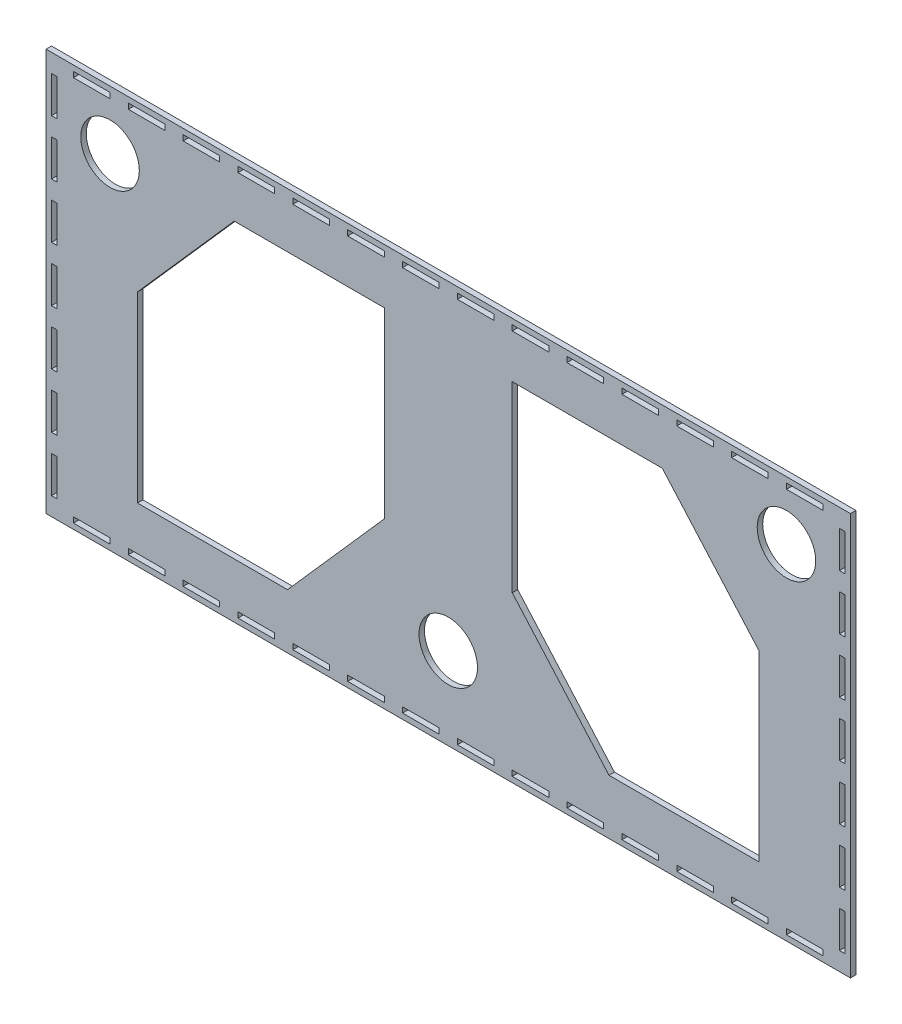
SolidWorks part; units mm, degrees
ref_plane "Plan de face" through (0, 0, 0) normal (0, 0, 1) x (1, 0, 0)
ref_plane "Plan de dessus" through (0, 0, 0) normal (0, 1, 0) x (1, 0, 0)
ref_plane "Plan de droite" through (0, 0, 0) normal (1, 0, 0) x (0, 0, -1)
sketch "Esquisse1" plane through (0, 0, 0) normal (0, 0, 1) x (1, 0, 0)
  line L1 (-220, 110) -> (220, 110)
  line L2 (-220, 110) -> (-220, -110)
  line L3 (-220, -110) -> (220, -110)
  line L4 (220, 110) -> (220, -110)
  line L5 (-220, 110) -> (220, -110) construction
  line L6 (-220, -110) -> (220, 110) construction
  point P0 (0, 0)
  dimension "D1" = 440
  dimension "D2" = 220
extrude "Boss.-Extru.1" add sketch "Esquisse1" along normal blind 3
sketch "Esquisse2" plane through (0, 0, 0) normal (0, 0, -1) x (-1, 0, 0)
  line L0 (0, 110) -> (0, -110) construction
  line L1 (-220, 110) -> (220, 110) construction
  line L2 (220, -110) -> (-220, -110) construction
  line L3 (-220, 0) -> (220, 0) construction
  line L4 (-220, -110) -> (-220, 110) construction
  line L5 (220, 110) -> (220, -110) construction
  circle A0 centre (-185, 78) radius 16
  circle A4 centre (185, 78) radius 16
  circle A7 centre (0, -65) radius 16
  point P18 (0, -66.7809)
  dimension "D1" = 32
  dimension "D2" = 32
  dimension "D3" = 35
  dimension "D5" = 32
  dimension "D4" = 45
extrude "Enlèv. mat._Tube" cut sketch "Esquisse2" against normal blind 3
sketch "Esquisse4" plane through (0, 0, 0) normal (0, 0, -1) x (-1, 0, 0)
  line L0 (-220, 110) -> (220, 110) construction
  line L1 (-205, 107) -> (-185, 107)
  line L2 (-205, 107) -> (-205, 104)
  line L3 (-205, 104) -> (-185, 104)
  line L4 (-185, 107) -> (-185, 104)
  line L5 (-220, -110) -> (-220, 110) construction
  line L6 (-175, 107) -> (-155, 107)
  line L7 (-175, 107) -> (-175, 104)
  line L8 (-175, 104) -> (-155, 104)
  line L9 (-155, 107) -> (-155, 104)
  line L10 (-145, 107) -> (-125, 107)
  line L11 (-145, 107) -> (-145, 104)
  line L12 (-145, 104) -> (-125, 104)
  line L13 (-125, 107) -> (-125, 104)
  line L14 (-115, 107) -> (-95, 107)
  line L15 (-115, 107) -> (-115, 104)
  line L16 (-115, 104) -> (-95, 104)
  line L17 (-95, 107) -> (-95, 104)
  line L18 (-85, 107) -> (-65, 107)
  line L19 (-85, 107) -> (-85, 104)
  line L20 (-85, 104) -> (-65, 104)
  line L21 (-65, 107) -> (-65, 104)
  line L22 (-55, 107) -> (-35, 107)
  line L23 (-55, 107) -> (-55, 104)
  line L24 (-55, 104) -> (-35, 104)
  line L25 (-35, 107) -> (-35, 104)
  line L26 (-25, 107) -> (-5, 107)
  line L27 (-25, 107) -> (-25, 104)
  line L28 (-25, 104) -> (-5, 104)
  line L29 (-5, 107) -> (-5, 104)
  line L30 (5, 107) -> (25, 107)
  line L31 (5, 107) -> (5, 104)
  line L32 (5, 104) -> (25, 104)
  line L33 (25, 107) -> (25, 104)
  line L34 (35, 107) -> (55, 107)
  line L35 (35, 107) -> (35, 104)
  line L36 (35, 104) -> (55, 104)
  line L37 (55, 107) -> (55, 104)
  line L38 (65, 107) -> (85, 107)
  line L39 (65, 107) -> (65, 104)
  line L40 (65, 104) -> (85, 104)
  line L41 (85, 107) -> (85, 104)
  line L42 (95, 107) -> (115, 107)
  line L43 (95, 107) -> (95, 104)
  line L44 (95, 104) -> (115, 104)
  line L45 (115, 107) -> (115, 104)
  line L46 (125, 107) -> (145, 107)
  line L47 (125, 107) -> (125, 104)
  line L48 (125, 104) -> (145, 104)
  line L49 (145, 107) -> (145, 104)
  line L50 (155, 107) -> (175, 107)
  line L51 (155, 107) -> (155, 104)
  line L52 (155, 104) -> (175, 104)
  line L53 (175, 107) -> (175, 104)
  line L54 (185, 107) -> (205, 107)
  line L55 (185, 107) -> (185, 104)
  line L56 (185, 104) -> (205, 104)
  line L57 (205, 107) -> (205, 104)
  line L58 (-245.8877, 0) -> (255.7593, 0) construction
  line L60 (220, -110) -> (-220, -110) construction
  line L61 (95, -107) -> (95, -104)
  line L62 (95, -104) -> (115, -104)
  line L63 (115, -107) -> (115, -104)
  line L64 (95, -107) -> (115, -107)
  line L65 (125, -107) -> (125, -104)
  line L66 (125, -104) -> (145, -104)
  line L67 (145, -107) -> (145, -104)
  line L68 (125, -107) -> (145, -107)
  line L69 (155, -107) -> (155, -104)
  line L70 (155, -104) -> (175, -104)
  line L71 (175, -107) -> (175, -104)
  line L72 (155, -107) -> (175, -107)
  line L73 (185, -107) -> (185, -104)
  line L74 (185, -104) -> (205, -104)
  line L75 (205, -107) -> (205, -104)
  line L76 (185, -107) -> (205, -107)
  line L77 (65, -107) -> (65, -104)
  line L78 (65, -104) -> (85, -104)
  line L79 (85, -107) -> (85, -104)
  line L80 (65, -107) -> (85, -107)
  line L81 (35, -107) -> (35, -104)
  line L82 (35, -104) -> (55, -104)
  line L83 (55, -107) -> (55, -104)
  line L84 (35, -107) -> (55, -107)
  line L85 (5, -107) -> (5, -104)
  line L86 (5, -104) -> (25, -104)
  line L87 (25, -107) -> (25, -104)
  line L88 (5, -107) -> (25, -107)
  line L89 (-25, -107) -> (-25, -104)
  line L90 (-25, -104) -> (-5, -104)
  line L91 (-5, -107) -> (-5, -104)
  line L92 (-25, -107) -> (-5, -107)
  line L93 (-55, -107) -> (-55, -104)
  line L94 (-55, -104) -> (-35, -104)
  line L95 (-35, -107) -> (-35, -104)
  line L96 (-55, -107) -> (-35, -107)
  line L97 (-85, -107) -> (-85, -104)
  line L98 (-85, -104) -> (-65, -104)
  line L99 (-65, -107) -> (-65, -104)
  line L100 (-85, -107) -> (-65, -107)
  line L101 (-115, -107) -> (-115, -104)
  line L102 (-115, -104) -> (-95, -104)
  line L103 (-95, -107) -> (-95, -104)
  line L104 (-115, -107) -> (-95, -107)
  line L105 (-145, -107) -> (-145, -104)
  line L106 (-145, -104) -> (-125, -104)
  line L107 (-125, -107) -> (-125, -104)
  line L108 (-145, -107) -> (-125, -107)
  line L109 (-175, -107) -> (-175, -104)
  line L110 (-175, -104) -> (-155, -104)
  line L111 (-155, -107) -> (-155, -104)
  line L112 (-175, -107) -> (-155, -107)
  line L113 (-205, -104) -> (-185, -104)
  line L114 (-185, -107) -> (-185, -104)
  line L115 (-205, -107) -> (-185, -107)
  line L116 (-205, -107) -> (-205, -104)
  dimension "D1" = 20
  dimension "D2" = 3
  dimension "D3" = 3
  dimension "D4" = 15
  dimension "D6" = 10
  dimension "D7" = 110
  dimension "D5" = 14
extrude "Enlèv. mat._CôtéArrièreBoite" cut sketch "Esquisse4" against normal blind 3
sketch "Esquisse5" plane through (0, 0, 0) normal (0, 0, -1) x (-1, 0, 0)
  line L0 (-220, -110) -> (-220, 110) construction
  line L1 (-217, -100) -> (-214, -100)
  line L2 (-217, -100) -> (-217, -80)
  line L3 (-217, -80) -> (-214, -80)
  line L4 (-214, -100) -> (-214, -80)
  line L5 (220, -110) -> (-220, -110) construction
  line L6 (0, 110) -> (0, -110) construction
  line L7 (-220, 110) -> (220, 110) construction
  line L8 (-217, -70) -> (-217, -50)
  line L9 (-217, -50) -> (-214, -50)
  line L10 (-214, -70) -> (-214, -50)
  line L11 (-217, -70) -> (-214, -70)
  line L12 (-217, -40) -> (-217, -20)
  line L13 (-217, -20) -> (-214, -20)
  line L14 (-214, -40) -> (-214, -20)
  line L15 (-217, -40) -> (-214, -40)
  line L16 (-217, -10) -> (-217, 10)
  line L17 (-217, 10) -> (-214, 10)
  line L18 (-214, -10) -> (-214, 10)
  line L19 (-217, -10) -> (-214, -10)
  line L20 (-217, 20) -> (-217, 40)
  line L21 (-217, 40) -> (-214, 40)
  line L22 (-214, 20) -> (-214, 40)
  line L23 (-217, 20) -> (-214, 20)
  line L24 (-217, 50) -> (-217, 70)
  line L25 (-217, 70) -> (-214, 70)
  line L26 (-214, 50) -> (-214, 70)
  line L27 (-217, 50) -> (-214, 50)
  line L28 (-217, 80) -> (-217, 100)
  line L29 (-217, 100) -> (-214, 100)
  line L30 (-214, 80) -> (-214, 100)
  line L31 (-217, 80) -> (-214, 80)
  line L80 (217, 80) -> (214, 80)
  line L81 (214, 80) -> (214, 100)
  line L82 (217, 100) -> (214, 100)
  line L83 (217, 80) -> (217, 100)
  line L84 (217, 50) -> (214, 50)
  line L85 (214, 50) -> (214, 70)
  line L86 (217, 70) -> (214, 70)
  line L87 (217, 50) -> (217, 70)
  line L88 (217, 20) -> (214, 20)
  line L89 (214, 20) -> (214, 40)
  line L90 (217, 40) -> (214, 40)
  line L91 (217, 20) -> (217, 40)
  line L92 (217, -10) -> (214, -10)
  line L93 (214, -10) -> (214, 10)
  line L94 (217, 10) -> (214, 10)
  line L95 (217, -10) -> (217, 10)
  line L96 (217, -40) -> (214, -40)
  line L97 (214, -40) -> (214, -20)
  line L98 (217, -20) -> (214, -20)
  line L99 (217, -40) -> (217, -20)
  line L100 (217, -70) -> (214, -70)
  line L101 (214, -70) -> (214, -50)
  line L102 (217, -50) -> (214, -50)
  line L103 (217, -70) -> (217, -50)
  line L104 (214, -100) -> (214, -80)
  line L105 (217, -80) -> (214, -80)
  line L106 (217, -100) -> (217, -80)
  line L107 (217, -100) -> (214, -100)
  dimension "D1" = 20
  dimension "D2" = 3
  dimension "D3" = 3
  dimension "D4" = 10
  dimension "D6" = 10
  dimension "D5" = 7
extrude "Enlèv. mat.-CôtéDGBoite" cut sketch "Esquisse5" against normal blind 3
sketch "Esquisse6" plane through (0, 0, 0) normal (0, 0, -1) x (-1, 0, 0)
  line L0 (0, 126.6946) -> (0, -167.4592) construction
  line L1 (-220, -110) -> (-220, 110) construction
  line L2 (-170, 80) -> (-35, 80) construction
  line L3 (-170, 80) -> (-170, -80) construction
  line L4 (-170, -80) -> (-35, -80) construction
  line L5 (-35, 80) -> (-35, -80) construction
  line L6 (-220, 110) -> (220, 110) construction
  line L7 (-170, 20) -> (-117.085, 80)
  line L8 (-170, 20) -> (-170, -80)
  line L9 (-117.085, 80) -> (-35, 80)
  line L16 (-87.915, -80) -> (-35, -20)
  line L17 (-35, 80) -> (-35, -20)
  line L18 (-170, -80) -> (-87.915, -80)
  line L20 (170, 20) -> (170, -80)
  line L21 (170, 20) -> (117.085, 80)
  line L22 (117.085, 80) -> (35, 80)
  line L23 (35, 80) -> (35, -20)
  line L24 (87.915, -80) -> (35, -20)
  line L25 (170, -80) -> (87.915, -80)
  dimension "D7" = 80
  dimension "D1" = 50
  dimension "D2" = 30
  dimension "D3" = 100
  dimension "D4" = 135
  dimension "D5" = 160
  dimension "D6" = 80
extrude "Enlèv. mat.-Extru.1" cut sketch "Esquisse6" against normal blind 3
